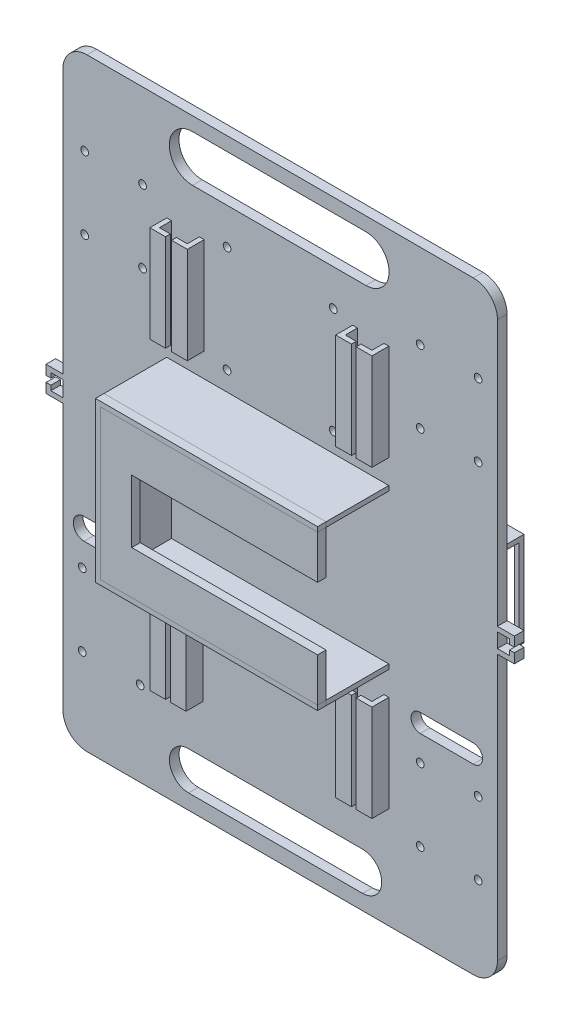
SolidWorks part; units mm, degrees
ref_plane "前视基准面" through (0, 0, 0) normal (0, 0, 1) x (1, 0, 0)
ref_plane "上视基准面" through (0, 0, 0) normal (0, 1, 0) x (1, 0, 0)
ref_plane "右视基准面" through (0, 0, 0) normal (1, 0, 0) x (0, 0, -1)
sketch "草图2" plane through (0, 0, 0) normal (0, 0, 1) x (1, 0, 0)
  line L0 (-107.1807, -135.5134) -> (-66.1807, -135.5134) construction
  line L1 (-97.1807, 63.077) -> (62.8193, 63.077)
  line L2 (-107.1807, 53.077) -> (-107.1807, -176.923)
  line L3 (-97.1807, -186.923) -> (62.8193, -186.923)
  line L4 (72.8193, 53.077) -> (72.8193, -176.923)
  line L5 (-92.3948, -186.923) -> (-92.3948, -116.923) construction
  line L6 (-85.9477, -186.923) -> (-85.9477, -156.923) construction
  line L7 (-107.1807, -156.923) -> (-66.1807, -156.923) construction
  line L8 (-107.1807, -116.923) -> (-66.1807, -116.923) construction
  line L9 (-66.1807, -116.923) -> (-66.1807, -156.923) construction
  line L10 (-66.1807, -156.923) -> (-107.1807, -156.923) construction
  line L11 (-107.1807, -156.923) -> (-107.1807, -116.923) construction
  line L12 (-107.1807, -156.923) -> (-107.1807, -158.923) construction
  line L13 (-107.1807, -152.2152) -> (-99.1807, -152.2152) construction
  line L14 (-99.1807, -156.923) -> (-99.1807, -151.923) construction
  line L15 (-99.1807, -151.923) -> (-99.1807, -121.923) construction
  line L16 (-99.1807, -121.923) -> (-75.1807, -121.923) construction
  line L17 (-75.1807, -121.923) -> (-75.1807, -151.923) construction
  line L18 (-66.1807, -156.923) -> (72.8193, -156.923) construction
  line L19 (-99.1807, -151.923) -> (72.8193, -151.923) construction
  line L20 (-99.1807, -121.923) -> (72.8193, -121.923) construction
  line L21 (72.8193, -151.923) -> (64.8193, -151.923) construction
  line L22 (64.8193, -151.923) -> (40.8193, -151.923) construction
  line L23 (40.8193, -151.923) -> (40.8193, -121.923) construction
  line L24 (40.8193, -121.923) -> (64.8193, -121.923) construction
  line L25 (64.8193, -121.923) -> (64.8193, -151.923) construction
  line L26 (-97.1807, 63.077) -> (-97.1807, 33.077) construction
  line L27 (-97.1807, 33.077) -> (-97.1807, -6.923) construction
  line L28 (-107.1807, 33.077) -> (-98.1807, 33.077) construction
  line L29 (-98.1807, 33.077) -> (-98.1807, 28.077) construction
  line L30 (-98.1807, 28.077) -> (-98.1807, -1.923) construction
  line L31 (-98.1807, 28.077) -> (-74.1807, 28.077) construction
  line L32 (-74.1807, 28.077) -> (-74.1807, -1.923) construction
  line L33 (-98.1807, -1.923) -> (-74.1807, -1.923) construction
  line L34 (-74.1807, 28.077) -> (72.8193, 28.077) construction
  line L35 (-74.1807, -1.923) -> (72.8193, -1.923) construction
  line L36 (40.8193, -121.923) -> (40.8193, 28.077) construction
  line L37 (64.8193, -121.923) -> (64.8193, 28.077) construction
  arc A0 (-97.1807, 63.077) -> (-107.1807, 53.077) centre (-97.1807, 53.077) ccw
  arc A1 (62.8193, 63.077) -> (72.8193, 53.077) centre (62.8193, 53.077) cw
  arc A2 (-107.1807, -176.923) -> (-97.1807, -186.923) centre (-97.1807, -176.923) ccw
  arc A3 (62.8193, -186.923) -> (72.8193, -176.923) centre (62.8193, -176.923) ccw
  circle A5 centre (-99.1807, -151.923) radius 1.6
  circle A6 centre (-99.1807, -121.923) radius 1.6
  circle A7 centre (-75.1807, -121.923) radius 1.6
  circle A8 centre (-75.1807, -151.923) radius 1.6
  circle A9 centre (64.8193, -151.923) radius 1.6
  circle A10 centre (40.8193, -151.923) radius 1.6
  circle A11 centre (40.8193, -121.923) radius 1.6
  circle A12 centre (64.8193, -121.923) radius 1.6
  circle A13 centre (-98.1807, 28.077) radius 1.6
  circle A14 centre (-98.1807, -1.923) radius 1.6
  circle A15 centre (-74.1807, 28.077) radius 1.6
  circle A16 centre (-74.1807, -1.923) radius 1.6
  circle A17 centre (40.8193, 28.077) radius 1.6
  circle A18 centre (64.8193, 28.077) radius 1.6
  circle A19 centre (40.8193, -1.923) radius 1.6
  circle A20 centre (64.8193, -1.923) radius 1.6
  point P6 (-107.1807, 63.077)
  point P9 (72.8193, 63.077)
  point P12 (-107.1807, -186.923)
  dimension "D3" = 10
  dimension "D4" = 10
  dimension "D5" = 10
  dimension "D6" = 10
  dimension "D13" = 30
  dimension "D14" = 24
  dimension "D15" = 8
  dimension "D16" = 24
  dimension "D17" = 30
  dimension "D21" = 30
  dimension "D22" = 24
  dimension "D1" = 180
  dimension "D2" = 250
  dimension "D7" = 41
  dimension "D8" = 70
  dimension "D9" = 30
  dimension "D10" = 41
  dimension "D11" = 8
  dimension "D12" = 5
  dimension "D18" = 40
  dimension "D19" = 9
  dimension "D20" = 5
extrude "凸台-拉伸1" add sketch "草图2" along normal blind 4
sketch "草图3" plane through (0, 0, 4) normal (0, 0, 1) x (1, 0, 0)
  line L0 (-17.1807, 63.077) -> (-17.1807, -186.923) construction
  line L1 (62.8193, 63.077) -> (-97.1807, 63.077) construction
  line L2 (-97.1807, -186.923) -> (62.8193, -186.923) construction
  line L3 (-107.1807, -61.923) -> (72.8193, -61.923) construction
  line L4 (-107.1807, 53.077) -> (-107.1807, -176.923) construction
  line L5 (72.8193, -176.923) -> (72.8193, 53.077) construction
  line L6 (-17.1807, -61.923) -> (-17.1807, -30.923) construction
  line L7 (-17.1807, -61.923) -> (-17.1807, -92.923) construction
  line L8 (-17.1807, -61.923) -> (27.8193, -61.923) construction
  line L9 (-17.1807, -61.923) -> (-62.1807, -61.923) construction
  line L10 (-17.1807, -30.923) -> (27.8193, -30.923) construction
  line L11 (27.8193, -30.923) -> (27.8193, -92.923) construction
  line L12 (27.8193, -92.923) -> (-62.1807, -92.923) construction
  line L13 (-62.1807, -92.923) -> (-62.1807, -30.923) construction
  line L14 (-62.1807, -30.923) -> (-17.1807, -30.923) construction
  line L15 (27.8193, -30.923) -> (-62.1807, -30.923)
  line L16 (-62.1807, -30.923) -> (-62.1807, -92.923)
  line L17 (-62.1807, -92.923) -> (27.8193, -92.923)
  line L18 (27.8193, -30.923) -> (27.8193, -28.923) construction
  line L19 (-62.1807, -30.923) -> (-64.1807, -30.923) construction
  line L20 (-62.1807, -92.923) -> (-62.1807, -94.923) construction
  line L21 (27.8193, -30.923) -> (27.8193, -28.923)
  line L22 (27.8193, -28.923) -> (-64.1807, -28.923)
  line L23 (-64.1807, -28.923) -> (-64.1807, -94.923)
  line L24 (-64.1807, -94.923) -> (27.8193, -94.923)
  line L25 (27.8193, -94.923) -> (27.8193, -92.923)
  dimension "D1" = 31
  dimension "D2" = 45
  dimension "D3" = 45
  dimension "D4" = 2
  dimension "D5" = 2
extrude "凸台-拉伸2" add sketch "草图3" along normal blind 26 contours L22 L23 L24 L25 L17 L16 L15 L21
sketch "草图5" plane through (0, 0, 30) normal (0, 0, 1) x (1, 0, 0)
  line L0 (-18.1807, -28.923) -> (-18.1807, -48.923) construction
  line L1 (27.8193, -28.923) -> (-64.1807, -28.923) construction
  line L2 (-18.1807, -94.923) -> (-18.1807, -74.923) construction
  line L3 (-64.1807, -94.923) -> (27.8193, -94.923) construction
  line L4 (27.8193, -28.923) -> (27.8193, -48.923)
  line L5 (27.8193, -48.923) -> (-64.1807, -48.923)
  line L6 (-64.1807, -28.923) -> (-64.1807, -94.923) construction
  line L7 (-64.1807, -48.923) -> (-64.1807, -28.923)
  line L8 (-64.1807, -28.923) -> (27.8193, -28.923)
  line L9 (27.8193, -94.923) -> (27.8193, -74.923)
  line L10 (27.8193, -74.923) -> (-64.1807, -74.923)
  line L11 (-64.1807, -28.923) -> (-64.1807, -94.923) construction
  line L12 (-64.1807, -74.923) -> (-64.1807, -94.923)
  line L13 (-64.1807, -94.923) -> (27.8193, -94.923)
  line L14 (-64.1807, -61.923) -> (-49.1807, -61.923) construction
  line L15 (-64.1807, -48.923) -> (-64.1807, -74.923)
  line L16 (-49.1807, -74.923) -> (-49.1807, -48.923)
  line L17 (-49.1807, -48.923) -> (-64.1807, -48.923)
  line M11 (27.8193, -92.923) -> (-62.1807, -92.923)
  line M12 (-62.1807, -92.923) -> (-62.1807, -30.923)
  line M13 (-62.1807, -30.923) -> (27.8193, -30.923)
  dimension "D1" = 15
extrude "凸台-拉伸3" add sketch "草图5" along normal blind 3.5 separate body contours L5 L4 M13 M12 | L9 L10 M12 M11 | L10 L16 L5 M12
sketch "草图6" plane through (0, 0, 33.5) normal (0, 0, 1) x (1, 0, 0)
  line L0 (27.8193, -30.923) -> (27.8193, -28.923)
  line L1 (27.8193, -28.923) -> (-64.1807, -28.923)
  line L2 (-64.1807, -28.923) -> (-64.1807, -94.923)
  line L3 (-64.1807, -94.923) -> (27.8193, -94.923)
  line L4 (27.8193, -94.923) -> (27.8193, -92.923)
  line L5 (27.8193, -92.923) -> (-62.1807, -92.923)
  line L6 (-62.1807, -92.923) -> (-62.1807, -30.923)
  line L7 (-62.1807, -30.923) -> (27.8193, -30.923)
extrude "凸台-拉伸4" add sketch "草图6" against normal blind 3.5 separate body
sketch "草图7" plane through (0, 0, 4) normal (0, 0, 1) x (1, 0, 0)
  line L0 (-64.1807, -94.923) -> (-64.1807, -104.923) construction
  line L1 (27.8193, -94.923) -> (27.8193, -104.923) construction
  line L2 (-64.1807, -104.923) -> (-64.1807, -144.923) construction
  line L3 (27.8193, -104.923) -> (27.8193, -144.923) construction
  line L4 (-64.1807, -104.923) -> (-62.1807, -104.923) construction
  line L5 (-62.1807, -104.923) -> (-62.1807, -144.923) construction
  line L6 (-62.1807, -144.923) -> (-64.1807, -144.923) construction
  line L7 (-64.1807, -144.923) -> (-64.1807, -104.923) construction
  line L8 (27.8193, -104.923) -> (25.8193, -104.923) construction
  line L9 (25.8193, -104.923) -> (25.8193, -144.923) construction
  line L10 (25.8193, -144.923) -> (27.8193, -144.923) construction
  line L11 (27.8193, -144.923) -> (27.8193, -104.923) construction
  line L12 (-64.1807, -104.923) -> (-49.1807, -104.923) construction
  line L13 (-49.1807, -104.923) -> (-49.1807, -144.923) construction
  line L14 (-49.1807, -144.923) -> (-51.1807, -144.923) construction
  line L15 (-51.1807, -144.923) -> (-51.1807, -104.923) construction
  line L16 (27.8193, -104.923) -> (12.8193, -104.923) construction
  line L17 (12.8193, -104.923) -> (12.8193, -144.923) construction
  line L18 (12.8193, -144.923) -> (27.8193, -144.923) construction
  line L19 (12.8193, -104.923) -> (14.8193, -104.923) construction
  line L20 (14.8193, -104.923) -> (14.8193, -144.923) construction
  line L21 (-64.1807, -104.923) -> (-62.1807, -104.923)
  line L22 (-62.1807, -104.923) -> (-62.1807, -144.923)
  line L23 (-62.1807, -144.923) -> (-64.1807, -144.923)
  line L24 (-64.1807, -144.923) -> (-64.1807, -104.923)
  line L25 (-51.1807, -104.923) -> (-51.1807, -144.923)
  line L26 (-51.1807, -144.923) -> (-49.1807, -144.923)
  line L27 (-49.1807, -144.923) -> (-49.1807, -104.923)
  line L28 (-49.1807, -104.923) -> (-51.1807, -104.923)
  line L29 (12.8193, -104.923) -> (12.8193, -144.923)
  line L30 (12.8193, -144.923) -> (14.8193, -144.923)
  line L31 (14.8193, -144.923) -> (14.8193, -104.923)
  line L32 (14.8193, -104.923) -> (12.8193, -104.923)
  line L33 (25.8193, -104.923) -> (27.8193, -104.923)
  line L34 (27.8193, -104.923) -> (27.8193, -144.923)
  line L35 (27.8193, -144.923) -> (25.8193, -144.923)
  line L36 (25.8193, -144.923) -> (25.8193, -104.923)
  dimension "D1" = 10
  dimension "D2" = 40
extrude "凸台-拉伸5" add sketch "草图7" along normal blind 5
sketch "草图8" plane through (0, 0, 9) normal (0, 0, 1) x (1, 0, 0)
  line L0 (-64.1807, -104.923) -> (-57.6807, -104.923)
  line L1 (-57.6807, -104.923) -> (-57.6807, -144.923)
  line L2 (-57.6807, -144.923) -> (-64.1807, -144.923)
  line L3 (-64.1807, -144.923) -> (-64.1807, -104.923)
  line L4 (-49.1807, -104.923) -> (-55.6807, -104.923)
  line L5 (-55.6807, -104.923) -> (-55.6807, -144.923)
  line L6 (-55.6807, -144.923) -> (-49.1807, -144.923)
  line L7 (-49.1807, -144.923) -> (-49.1807, -104.923)
  line L8 (12.8193, -104.923) -> (19.3193, -104.923)
  line L9 (19.3193, -104.923) -> (19.3193, -144.923)
  line L10 (19.3193, -144.923) -> (12.8193, -144.923)
  line L11 (12.8193, -144.923) -> (12.8193, -104.923)
  line L12 (27.8193, -104.923) -> (21.3193, -104.923)
  line L13 (21.3193, -144.923) -> (27.8193, -144.923)
  line L14 (27.8193, -144.923) -> (27.8193, -104.923)
  line L15 (21.3193, -104.923) -> (21.3193, -144.923)
extrude "凸台-拉伸6" add sketch "草图8" along normal blind 2
ref_plane "基准面1" through (-57.6807, -144.923, 9) normal (0, 0, -1) x (-1, 0, 0)
sketch "草图11" plane through (0, 0, 4) normal (0, 0, 1) x (1, 0, 0)
  line L0 (-64.1807, -28.923) -> (-64.1807, -18.923) construction
  line L1 (27.8193, -28.923) -> (27.8193, -18.923) construction
  line L2 (-64.1807, -18.923) -> (-64.1807, 21.077)
  line L3 (-64.1807, 21.077) -> (-62.1807, 21.077)
  line L4 (-62.1807, 21.077) -> (-62.1807, -18.923)
  line L5 (-62.1807, -18.923) -> (-64.1807, -18.923) construction
  line L6 (-64.1807, 21.077) -> (-48.649, 21.077) construction
  line L7 (-48.649, 21.077) -> (-50.649, 21.077)
  line L8 (-50.649, 21.077) -> (-50.649, -18.923)
  line L9 (-50.649, -18.923) -> (-48.649, -18.923)
  line L10 (-48.649, -18.923) -> (-48.649, 21.077)
  line L11 (27.8193, -18.923) -> (27.8193, 21.077)
  line L12 (27.8193, 21.077) -> (25.8193, 21.077)
  line L13 (25.8193, 21.077) -> (25.8193, -18.923)
  line L14 (25.8193, -18.923) -> (27.8193, -18.923)
  line L15 (27.8193, 21.077) -> (12.8193, 21.077) construction
  line L16 (12.8193, 21.077) -> (12.8193, -18.923)
  line L17 (12.8193, -18.923) -> (14.8193, -18.923)
  line L18 (14.8193, -18.923) -> (14.8193, 21.077)
  line L19 (14.8193, 21.077) -> (12.8193, 21.077)
extrude "凸台-拉伸7" add sketch "草图11" along normal blind 5 contours L10 L7 L8 L9 | L16 L17 L18 L19 | L13 L14 L11 L12
sketch "草图12" plane through (0, 0, 4) normal (0, 0, 1) x (1, 0, 0)
  line L0 (-64.1807, -28.923) -> (-64.1807, 21.077) construction
  line L1 (-64.1807, 21.077) -> (-62.1807, 21.077)
  line L2 (-62.1807, 21.077) -> (-62.1807, -18.923)
  line L3 (-62.1807, -18.923) -> (-64.1807, -18.923)
  line L4 (-64.1807, -18.923) -> (-64.1807, 21.077)
extrude "凸台-拉伸8" add sketch "草图12" along normal blind 5
sketch "草图13" plane through (0, 0, 9) normal (0, 0, 1) x (1, 0, 0)
  line L0 (-64.1807, 21.077) -> (-57.6807, 21.077)
  line L1 (-57.6807, 21.077) -> (-57.6807, -18.923)
  line L2 (-57.6807, -18.923) -> (-64.1807, -18.923)
  line L3 (-64.1807, 21.077) -> (-64.1807, -18.923) construction
  line L4 (-64.1807, -18.923) -> (-62.1807, -18.923) construction
  line L5 (-64.1807, -18.923) -> (-64.1807, 21.077)
extrude "凸台-拉伸9" add sketch "草图13" along normal blind 2
sketch "草图14" plane through (0, 0, 9) normal (0, 0, 1) x (1, 0, 0)
  line L0 (-48.649, 21.077) -> (-48.649, -18.923)
  line L1 (-48.649, -18.923) -> (-55.149, -18.923)
  line L2 (-55.149, -18.923) -> (-55.149, 21.077)
  line L3 (-55.149, 21.077) -> (-48.649, 21.077)
  line L4 (27.8193, -18.923) -> (21.3193, -18.923)
  line L5 (21.3193, -18.923) -> (21.3193, 21.077)
  line L6 (21.3193, 21.077) -> (27.8193, 21.077)
  line L7 (27.8193, 21.077) -> (27.8193, -18.923)
  line L8 (12.8193, -18.923) -> (19.3193, -18.923)
  line L9 (19.3193, -18.923) -> (19.3193, 21.077)
  line L10 (19.3193, 21.077) -> (12.8193, 21.077)
  line L11 (12.8193, 21.077) -> (12.8193, -18.923)
extrude "凸台-拉伸10" add sketch "草图14" along normal blind 2
sketch "草图16" plane through (0, 0, 0) normal (0, 0, -1) x (-1, 0, 0)
  line L0 (17.1807, 63.077) -> (17.1807, 23.077) construction
  line L1 (-62.8193, 63.077) -> (97.1807, 63.077) construction
  line L2 (17.1807, 23.077) -> (39.1807, 23.077) construction
  line L3 (17.1807, 23.077) -> (-4.8193, 23.077) construction
  line L4 (-4.8193, 23.077) -> (-4.8193, -20.923) construction
  line L5 (-4.8193, -20.923) -> (39.1807, -20.923) construction
  line L6 (39.1807, -20.923) -> (39.1807, 23.077) construction
  circle A0 centre (-4.8193, 23.077) radius 1.6
  circle A1 centre (39.1807, 23.077) radius 1.6
  circle A2 centre (39.1807, -20.923) radius 1.6
  circle A3 centre (-4.8193, -20.923) radius 1.6
extrude "切除-拉伸1" cut sketch "草图16" against normal blind 5
sketch "草图19" plane through (0, 0, 0) normal (0, 0, -1) x (-1, 0, 0)
  line L0 (-72.8193, -61.923) -> (107.1807, -61.923) construction
  line L1 (-72.8193, -176.923) -> (-72.8193, 53.077) construction
  line L2 (107.1807, 53.077) -> (107.1807, -176.923) construction
  line L3 (-72.8193, -61.923) -> (-32.7734, -61.923) construction
sketch "草图20" plane through (0, 0, 0) normal (0, 0, -1) x (-1, 0, 0)
  line L0 (-72.8193, -61.923) -> (-57.8193, -61.923) construction
  line L1 (-72.8193, -61.923) -> (107.1807, -61.923) construction
  line L2 (-57.8193, -61.923) -> (-22.8193, -61.923) construction
  line L3 (-22.8193, -61.923) -> (-22.8193, -44.423) construction
  line L4 (-22.8193, -61.923) -> (-22.8193, -79.423) construction
  line L5 (-22.8193, -79.423) -> (-57.8193, -79.423)
  line L6 (-57.8193, -79.423) -> (-57.8193, -44.423)
  line L7 (-57.8193, -44.423) -> (-22.8193, -44.423)
  line L8 (-22.8193, -44.423) -> (-22.8193, -79.423)
  line L9 (-22.8193, -44.423) -> (-22.8193, -42.423) construction
  line L10 (-57.8193, -44.423) -> (-59.8193, -44.423) construction
  line L11 (-57.8193, -79.423) -> (-57.8193, -81.423) construction
  line L12 (-22.8193, -79.423) -> (-20.8193, -79.423) construction
  line L13 (-22.8193, -42.423) -> (-59.8193, -42.423)
  line L14 (-59.8193, -42.423) -> (-59.8193, -81.423)
  line L15 (-59.8193, -81.423) -> (-20.8193, -81.423)
  line L16 (-20.8193, -81.423) -> (-20.8193, -42.423)
  line L17 (-20.8193, -42.423) -> (-22.8193, -42.423)
  dimension "D1" = 15
extrude "凸台-拉伸12" add sketch "草图20" along normal blind 20
sketch "草图21" plane through (20.8193, 0, 0) normal (-1, 0, 0) x (0, 0, 1)
  line L0 (0, -42.423) -> (0, -44.423) construction
  line L1 (0, 53.077) -> (0, -176.923) construction
  line L2 (0, -81.423) -> (0, -79.423) construction
  line L3 (0, -44.423) -> (-18, -44.423) construction
  line L4 (-18, -44.423) -> (-18, -79.423) construction
  line L5 (-18, -79.423) -> (0, -79.423) construction
  line L7 (0, -44.423) -> (-18, -44.423)
  line L8 (0, -44.423) -> (0, -79.423)
  line L9 (0, -79.423) -> (-18, -79.423)
  line L10 (-18, -44.423) -> (-18, -79.423)
extrude "切除-拉伸2" cut sketch "草图21" against normal blind 60
sketch "草图22" plane through (59.8193, 0, 0) normal (1, 0, 0) x (0, 0, -1)
  line L0 (18, -79.423) -> (0, -79.423) construction
  line L1 (0, -44.423) -> (3, -44.423)
  line L2 (0, -44.423) -> (0, -79.423)
  line L3 (0, -79.423) -> (3, -79.423)
  line L4 (3, -44.423) -> (3, -79.423)
  dimension "D1" = 3
extrude "凸台-拉伸13" add sketch "草图22" against normal blind 1
sketch "草图23" plane through (20.8193, 0, 0) normal (-1, 0, 0) x (0, 0, 1)
  line L1 (0, -44.423) -> (-3, -44.423)
  line L2 (0, -44.423) -> (0, -79.423)
  line L3 (0, -79.423) -> (-3, -79.423)
  line L4 (-3, -44.423) -> (-3, -79.423)
extrude "凸台-拉伸18" add sketch "草图23" against normal blind 1
sketch "草图24" plane through (0, 0, 0) normal (0, 0, -1) x (-1, 0, 0)
  line L0 (107.1807, -61.923) -> (92.1807, -61.923) construction
  line L1 (-72.8193, -61.923) -> (107.1807, -61.923) construction
  line L2 (92.1807, -61.923) -> (92.1807, -44.423) construction
  line L3 (92.1807, -44.423) -> (57.1807, -44.423) construction
  line L4 (57.1807, -44.423) -> (57.1807, -79.423) construction
  line L5 (57.1807, -79.423) -> (92.1807, -79.423) construction
  line L6 (92.1807, -79.423) -> (92.1807, -61.923) construction
  line L7 (92.1807, -44.423) -> (92.1807, -42.423) construction
  line L8 (92.1807, -44.423) -> (57.1807, -44.423)
  line L9 (92.1807, -44.423) -> (92.1807, -79.423)
  line L10 (92.1807, -79.423) -> (57.1807, -79.423)
  line L11 (57.1807, -44.423) -> (57.1807, -79.423)
  line L12 (92.1807, -44.423) -> (94.1807, -44.423) construction
  line L14 (93.8137, -42.423) -> (54.8137, -42.423)
  line L15 (93.8137, -42.423) -> (93.8137, -81.423)
  line L16 (93.8137, -81.423) -> (54.8137, -81.423)
  line L17 (54.8137, -42.423) -> (54.8137, -81.423)
  dimension "D1" = 39
  dimension "D2" = 39
extrude "凸台-拉伸19" add sketch "草图24" along normal blind 20
sketch "草图25" plane through (-93.8137, 0, 0) normal (-1, 0, 0) x (0, 0, 1)
  line L0 (0, -42.423) -> (-3, -42.423) construction
  line L1 (-20, -42.423) -> (0, -42.423) construction
  line L2 (0, -81.423) -> (-3, -81.423) construction
  line L3 (-20, -81.423) -> (0, -81.423) construction
  line L4 (-3, -81.423) -> (-3, -76.423) construction
  line L5 (-3, -42.423) -> (-3, -44.423) construction
  line L6 (-20, -44.423) -> (-15, -44.423)
  line L7 (-20, -76.423) -> (-15, -76.423) construction
  line L8 (-20, -81.423) -> (-20, -42.423) construction
  line L10 (-15, -44.423) -> (-3, -44.423)
  line L11 (-15, -44.423) -> (-15, -76.423)
  line L12 (-15, -76.423) -> (-3, -76.423)
  line L13 (-3, -44.423) -> (-3, -76.423)
  dimension "D1" = 5
extrude "切除-拉伸3" cut sketch "草图25" against normal blind 50 contours L13 L10 L11 L12
sketch "草图26" plane through (72.8193, 0, 0) normal (1, 0, 0) x (0, 0, -1)
  line L0 (-4, -56.923) -> (0, -56.923)
  line L1 (0, -42.423) -> (0, -81.423) construction
  line L2 (0, -176.923) -> (0, 53.077) construction
  line L3 (0, -61.923) -> (0, -66.923) construction
  line L4 (0, -56.923) -> (-4, -56.923) construction
  line L5 (-4, -176.923) -> (-4, 53.077) construction
  line L6 (-4, -56.923) -> (-4, -58.923) construction
  line L7 (0, -66.923) -> (-4, -66.923) construction
  line L8 (-4, -66.923) -> (-4, -64.923) construction
  line L9 (0, -58.923) -> (-4, -58.923)
  line L13 (0, -56.923) -> (0, -58.923)
  line L14 (0, -66.923) -> (-4, -66.923)
  line L15 (0, -66.923) -> (0, -64.923)
  line L16 (0, -64.923) -> (-4, -64.923)
  line L17 (-4, -66.923) -> (-4, -64.923)
  line L18 (-4, -58.923) -> (-4, -56.923)
extrude "凸台-拉伸20" add sketch "草图26" along normal blind 5
sketch "草图27" plane through (77.8193, 0, 0) normal (1, 0, 0) x (0, 0, -1)
  line L0 (-4, -56.923) -> (-4, -60.923)
  line L1 (-4, -64.923) -> (-4, -58.923) construction
  line L2 (-4, -60.923) -> (0, -60.923)
  line L3 (0, -64.923) -> (0, -58.923) construction
  line L4 (0, -60.923) -> (0, -56.923)
  line L5 (0, -56.923) -> (-4, -56.923)
  line L6 (-4, -66.923) -> (-4, -62.923)
  line L7 (-4, -62.923) -> (0, -62.923)
  line L8 (0, -42.423) -> (0, -81.423) construction
  line L9 (0, -62.923) -> (0, -66.923)
  line L10 (0, -66.923) -> (-4, -66.923)
extrude "凸台-拉伸21" add sketch "草图27" along normal blind 2
sketch "草图28" plane through (-107.1807, 0, 0) normal (-1, 0, 0) x (0, 0, 1)
  line L0 (0, -61.923) -> (0, -56.402) construction
  line L2 (0, -81.423) -> (0, -42.423) construction
  line L3 (0, -61.923) -> (0, -66.923) construction
  line L4 (0, -56.402) -> (0, -58.402)
  line L5 (0, -58.402) -> (4, -58.402)
  line L6 (4, -28.923) -> (4, -94.923) construction
  line L7 (4, -58.402) -> (4, -56.402)
  line L8 (4, -56.402) -> (0, -56.402)
  line L9 (0, -66.923) -> (0, -64.923)
  line L10 (0, -64.923) -> (4, -64.923)
  line L11 (4, 53.077) -> (4, -176.923) construction
  line L12 (4, -64.923) -> (4, -66.923)
  line L13 (4, -66.923) -> (0, -66.923)
extrude "凸台-拉伸22" add sketch "草图28" along normal blind 5
sketch "草图29" plane through (-112.1807, 0, 0) normal (-1, 0, 0) x (0, 0, 1)
  line L0 (0, -56.402) -> (0, -60.402)
  line L1 (0, -58.402) -> (0, -64.923) construction
  line L2 (0, -60.402) -> (4, -60.402)
  line L3 (4, -58.402) -> (4, -64.923) construction
  line L4 (4, -60.402) -> (4, -56.402)
  line L5 (4, -56.402) -> (0, -56.402)
  line L6 (0, -66.923) -> (0, -62.923)
  line L7 (0, -62.923) -> (4, -62.923)
  line L8 (4, -62.923) -> (4, -66.923)
  line L9 (4, -28.923) -> (4, -94.923) construction
  line L10 (4, -66.923) -> (0, -66.923)
extrude "凸台-拉伸23" add sketch "草图29" along normal blind 2
sketch "草图31" plane through (0, 0, 0) normal (0, 0, -1) x (-1, 0, 0)
  line L0 (17.1807, 63.077) -> (17.1807, -186.923) construction
  line L1 (-62.8193, 63.077) -> (97.1807, 63.077) construction
  line L2 (97.1807, -186.923) -> (-62.8193, -186.923) construction
sketch "草图33" plane through (0, 0, 4) normal (0, 0, 1) x (1, 0, 0)
  line L0 (-53.4785, 47.7407) -> (18.307, 47.7407) construction
  line L1 (-53.4785, 57.3732) -> (18.307, 57.3732)
  line L2 (-53.4785, 38.1081) -> (18.307, 38.1081)
  line L3 (-55.1285, -172.7462) -> (16.9321, -172.7462) construction
  line L4 (-55.1285, -164.8151) -> (16.9321, -164.8151)
  line L5 (-55.1285, -180.6774) -> (16.9321, -180.6774)
  arc A0 (-53.4785, 57.3732) -> (-53.4785, 38.1081) centre (-53.4785, 47.7407) ccw
  arc A1 (18.307, 38.1081) -> (18.307, 57.3732) centre (18.307, 47.7407) ccw
  arc A2 (-55.1285, -164.8151) -> (-55.1285, -180.6774) centre (-55.1285, -172.7462) ccw
  arc A3 (16.9321, -180.6774) -> (16.9321, -164.8151) centre (16.9321, -172.7462) ccw
  point P2 (-17.5857, 47.7407)
  point P7 (-19.0982, -172.7462)
extrude "切除-拉伸4" cut sketch "草图33" against normal blind 10
sketch "草图34" plane through (0, 0, 4) normal (0, 0, 1) x (1, 0, 0)
  line L0 (-98.42, -107.5663) -> (-76.2578, -107.5663) construction
  line L1 (-98.42, -103.1076) -> (-76.2578, -103.1076)
  line L2 (-98.42, -112.0249) -> (-76.2578, -112.0249)
  line L3 (40.8291, -107.5663) -> (62.8404, -107.5663) construction
  line L4 (40.8291, -103.7723) -> (62.8404, -103.7723)
  line L5 (40.8291, -111.3603) -> (62.8404, -111.3603)
  arc A0 (-98.42, -103.1076) -> (-98.42, -112.0249) centre (-98.42, -107.5663) ccw
  arc A1 (-76.2578, -112.0249) -> (-76.2578, -103.1076) centre (-76.2578, -107.5663) ccw
  arc A2 (40.8291, -103.7723) -> (40.8291, -111.3603) centre (40.8291, -107.5663) ccw
  arc A3 (62.8404, -111.3603) -> (62.8404, -103.7723) centre (62.8404, -107.5663) ccw
  point P2 (-87.3389, -107.5663)
  point P7 (51.8348, -107.5663)
extrude "切除-拉伸5" cut sketch "草图34" against normal blind 10
